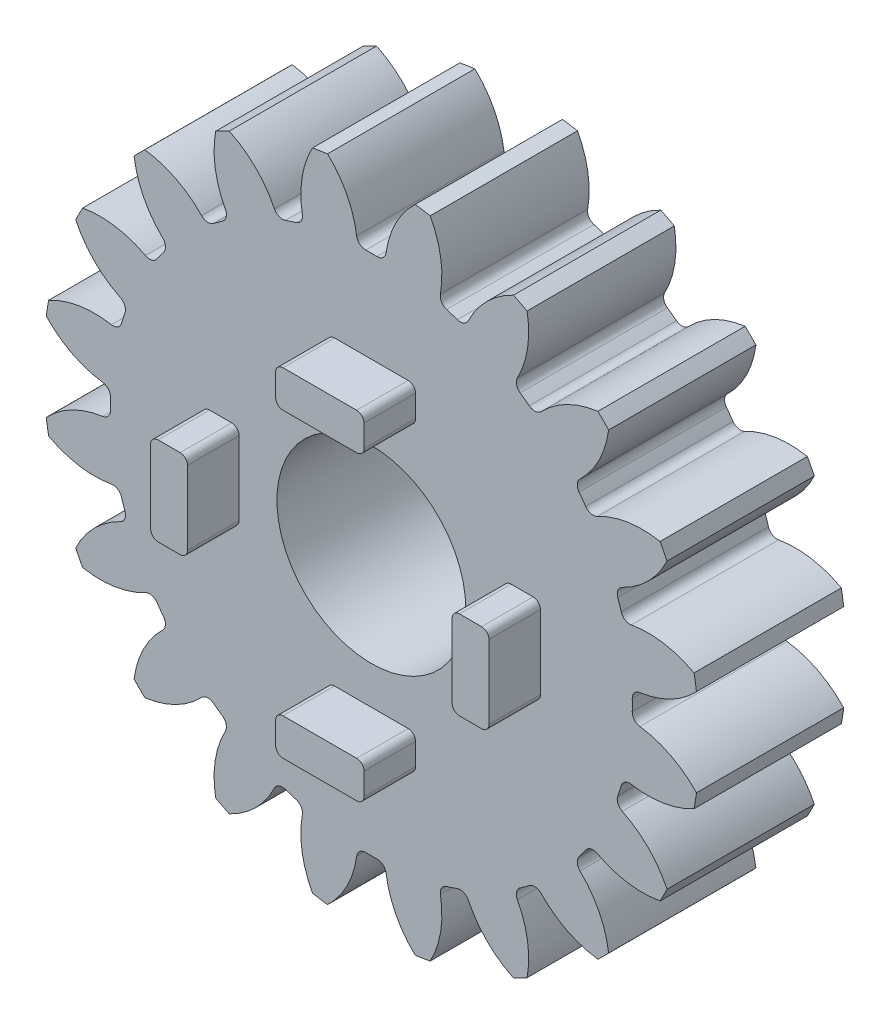
SolidWorks part; units mm, degrees
material "Custom Plastic"
ref_plane "Front Plane" through (0, 0, 0) normal (0, 0, 1) x (1, 0, 0)
ref_plane "Top Plane" through (0, 0, 0) normal (0, 1, 0) x (1, 0, 0)
ref_plane "Right Plane" through (0, 0, 0) normal (1, 0, 0) x (0, 0, -1)
sketch "Sketch1" plane through (0, 0, 0) normal (0, 0, 1) x (1, 0, 0)
  circle A0 centre (0, 0) radius 20.25
  circle A1 centre (0, 0) radius 22.275
  circle A2 centre (0, 0) radius 17.7188
  dimension "D1" = 40.5
  dimension "D3" = 35.4375
  dimension "D2" = 2.025
extrude "Boss-Extrude1" add sketch "Sketch1" along normal blind 10 contours A1
sketch "Sketch2" plane through (0, 0, 0) normal (0, 0, 1) x (1, 0, 0)
  line L0 (0, 0) -> (0, 22.275) construction
  line L1 (-1.5888, 20.1876) -> (1.5888, 20.1876) construction
  line L2 (-0.9452, 17.6935) -> (0, 0) construction
  line L3 (-2.3228, 22.3044) -> (0, 15.9226) construction
  line L4 (0, 0) -> (3.4846, 22.0008) construction
  line L5 (1.5888, 20.1876) -> (4.7273, 19.6905) construction
  circle A0 centre (0, 0) radius 22.275 construction
  arc A1 (-3.1164, 22.2074) -> (-0.9452, 17.6935) centre (-7.4448, 17.3463) cw
  arc A2 (3.1164, 22.2074) -> (0.9452, 17.6935) centre (7.4448, 17.3463) ccw
  circle A3 centre (0, 0) radius 17.7188 construction
  arc A4 (0.9452, 17.6935) -> (-0.9452, 17.6935) centre (0, 0) ccw
  circle A7 centre (0, 0) radius 20.25 construction
  circle A8 centre (0, 0) radius 22.425
  arc A9 (3.1164, 22.2074) -> (-3.1164, 22.2074) centre (0, 0) ccw
  circle A10 centre (0, 0) radius 22.275 construction
  dimension "D2" = 20
  dimension "D3" = 9
  dimension "D1" = 0.15
extrude "Cut-Extrude1" cut sketch "Sketch2" along normal through all
fillet "Fillet1" radius 0.6075 2 edges at (0.9452, 17.6935, 5) (-0.9452, 17.6935, 5)
pattern_circular "CirPattern5" count 20 over 360 about axis through (0, 0, 0) along (0, 0, 1) of "Cut-Extrude1", "Fillet1"
sketch "Sketch3" plane through (0, 0, 10) normal (0, 0, 1) x (1, 0, 0)
  circle A0 centre (0, 0) radius 6.4135
  dimension "D1" = 12.827
extrude "Cut-Extrude2" cut sketch "Sketch3" against normal blind 10
sketch "Sketch4" plane through (0, 0, 10) normal (0, 0, 1) x (1, 0, 0)
  line L1 (3, 11.4843) -> (-3, 11.4843)
  line L2 (3, 11.4843) -> (3, 8.9843)
  line L3 (3, 8.9843) -> (-3, 8.9843)
  line L4 (-3, 11.4843) -> (-3, 8.9843)
  line L5 (3, 11.4843) -> (-3, 8.9843) construction
  line L6 (3, 8.9843) -> (-3, 11.4843) construction
  circle A0 centre (0, 0) radius 10.2343 construction
  point P3 (0, 10.2343)
  dimension "D1" = 2.5
  dimension "D2" = 6
extrude "Boss-Extrude2" add sketch "Sketch4" along normal blind 3.5
fillet "Fillet2" radius 0.5 4 edges at (3, 11.4843, 11.75) (3, 8.9843, 11.75) (-3, 11.4843, 11.75) (-3, 8.9843, 11.75)
pattern_circular "CirPattern6" count 4 over 360 about axis through (0, 0, 0) along (0, 0, 1) of "Boss-Extrude2", "Fillet2"
equation "\"Reference Diameter\"= 40.5mm"
equation "\"Pressure Angle\"= 20'Degrees"
equation "\"number of teeth\"= 20"
equation "\"module\"= \"Reference Diameter\" / \"number of teeth\""
equation "\"base diameter\"= \"Reference Diameter\" * cos ( \"Pressure Angle\" )"
equation "\"addendum\"= \"module\""
equation "\"tooth depth\"= 2.25 * \"module\""
equation "\"tip diameter\"= \"Reference Diameter\" + 2 * \"module\""
equation "\"root diameter\"= \"Reference Diameter\" - 2.5 * \"module\""
equation "\"D1@Sketch1\"=\"Reference Diameter\""
equation "\"D2@Sketch1\"=\"addendum\""
equation "\"D3@Sketch1\"=\"root diameter\""
equation "\"D3@Sketch2\"=180 / \"number of teeth\""
equation "\"D1@Fillet1\"=0.3 * \"module\""
